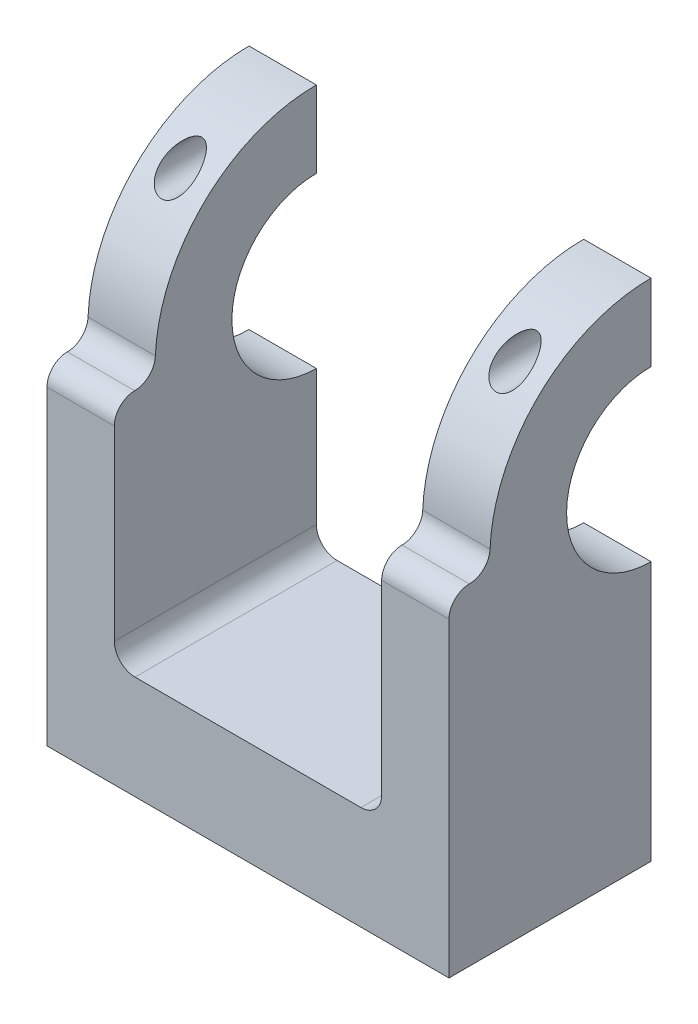
SolidWorks part; units mm, degrees
ref_plane "Front Plane" through (0, 0, 0) normal (0, 0, 1) x (1, 0, 0)
ref_plane "Top Plane" through (0, 0, 0) normal (0, 1, 0) x (1, 0, 0)
ref_plane "Right Plane" through (0, 0, 0) normal (1, 0, 0) x (0, 0, -1)
sketch "Sketch1" plane through (0, 0, 0) normal (1, 0, 0) x (0, 0, -1)
  circle A0 centre (0, 0) radius 8
  dimension "D1" = 16
sketch3d "3DSketch1" plane through (0, 0, 0) normal (0, 0, 1) x (1, 0, 0)
  dimension "D1" = 32.3
sketch "Sketch2" plane through (32.3, 0, 0) normal (1, 0, 0) x (0, 0, -1)
  circle A2 centre (0, 0) radius 8.15
  circle A3 centre (0, 0) radius 15.55
  dimension "D1" = 16.3
  dimension "D2" = 7.4
sketch "Sketch3" plane through (0, 0, 0) normal (1, 0, 0) x (0, 0, -1)
  circle A0 centre (0, 0) radius 8.15
  circle A1 centre (0, 0) radius 15.55
  dimension "D1" = 16.3
  dimension "D2" = 7.4
extrude "Boss-Extrude4" add sketch "Sketch3" along normal blind 6.5 separate body
extrude "Boss-Extrude5" add sketch "Sketch2" along normal blind 6.5
sketch "Sketch4" plane through (0, 0, 0) normal (1, 0, 0) x (0, 0, -1)
  line L0 (0, 15.55) -> (0, -15.55)
  circle A0 centre (0, 0) radius 15.55 construction
  arc A1 (0, -15.55) -> (0, 15.55) centre (0, 0) ccw
extrude "Cut-Extrude1" cut sketch "Sketch4" along normal up to surface (38.8 mm away) up to face at (38.8, 0, -15.55)
sketch "Sketch5" plane through (0, 0, 0) normal (0, 0, -1) x (-1, 0, 0)
  line L0 (-35.55, 15.55) -> (-35.55, 8.15) construction
  line L1 (-38.8, 15.55) -> (-32.3, 15.55) construction
  line L2 (-32.3, 8.15) -> (-38.8, 8.15) construction
  line L3 (-38.8, 11.85) -> (-32.3, 11.85) construction
  line L4 (-38.8, 15.55) -> (-38.8, 8.15) construction
  line L5 (-32.3, 8.15) -> (-32.3, 15.55) construction
  line L6 (-3.25, 15.55) -> (-3.25, 8.15) construction
  line L7 (0, 15.55) -> (-6.5, 15.55) construction
  line L8 (0, 8.15) -> (-6.5, 8.15) construction
  line L9 (-6.5, 11.85) -> (0, 11.85) construction
  line L10 (-6.5, 8.15) -> (-6.5, 15.55) construction
  line L11 (0, 15.55) -> (0, 8.15) construction
  circle A0 centre (-35.55, 11.85) radius 1.6
  circle A1 centre (-3.25, 11.85) radius 1.6
  dimension "D1" = 3.2
  dimension "D2" = 3.2
extrude "Cut-Extrude2" cut sketch "Sketch5" against normal through all
sketch "Sketch6" plane through (32.3, 0, 0) normal (-1, 0, 0) x (0, 0, 1)
  circle A0 centre (0, 0) radius 15.5 construction
  dimension "D1" = 31
sketch "Sketch7" plane through (6.5, 0, 0) normal (1, 0, 0) x (0, 0, -1)
  circle A0 centre (0, 0) radius 19.2 construction
  dimension "D1" = 38.4
sketch "Sketch8" plane through (38.8, 0, 0) normal (1, 0, 0) x (0, 0, -1)
  line L0 (0, 15.55) -> (0, 8.15) construction
  line L1 (0, -8.15) -> (0, -15.55) construction
  line L2 (0, 15.55) -> (0, 8.15)
  line L3 (0, -8.15) -> (0, -15.55)
  line L4 (-15.5, 0) -> (-15.5, -23.2)
  line L5 (0, -15.55) -> (0, -23.2)
  line L6 (-15.5, -23.2) -> (0, -23.2)
  circle A0 centre (0, 0) radius 15.5 construction
  circle A1 centre (0, 0) radius 15.5
  circle A2 centre (0, 0) radius 19.2 construction
  circle A3 centre (0, 0) radius 19.2
  point P7 (-15.5, 0)
  point P14 (0, -19.2)
  arc M1 (0, 15.55) -> (0, -15.55) centre (0, 0) ccw
  dimension "D1" = 4
extrude "Boss-Extrude6" add sketch "Sketch8" against normal up to surface (6.5 mm away) contours A3 L4 L6 L5 | L4 A3 L5 M1 up to face at (32.3, 0, 5.925)
sketch "Sketch9" plane through (0, 0, 15.5) normal (0, 0, 1) x (1, 0, 0)
  line L4 (38.8, -1.246) -> (32.3, -1.246)
  line L5 (32.3, -1.246) -> (32.3, -23.2)
  line L6 (32.3, -23.2) -> (38.8, -23.2)
  line L7 (38.8, -23.2) -> (38.8, -1.246)
  line L10 (32.3, -1.246) -> (32.3, -23.2)
  line L11 (32.3, -23.2) -> (38.8, -23.2)
  line L12 (38.8, -23.2) -> (38.8, -1.246)
  line L15 (38.8, -1.246) -> (32.3, -1.246)
  dimension "D1" = 0
extrude "Boss-Extrude7" add sketch "Sketch9" along normal blind 4
sketch "Sketch11" plane through (0, 0, 0) normal (-1, 0, 0) x (0, 0, 1)
  line L0 (0, -15.55) -> (0, -23.2) construction
  line L1 (15.5, -23.2) -> (0, -23.2) construction
  line L2 (15.5, 0) -> (15.5, -23.2) construction
  line L3 (0, -15.55) -> (0, -23.2)
  line L4 (15.5, -23.2) -> (0, -23.2)
  line L5 (15.5, 0) -> (15.5, -23.2)
  circle A0 centre (0, 0) radius 15.5 construction
  circle A1 centre (0, 0) radius 15.5
  arc M2 (0, -15.55) -> (0, 15.55) centre (0, 0) ccw
extrude "Boss-Extrude8" add sketch "Sketch11" against normal up to surface (6.5 mm away) contours L5 L3 L4 M2 up to face at (6.5, 0, 5.925)
sketch "Sketch12" plane through (0, 0, 15.5) normal (0, 0, 1) x (1, 0, 0)
  line L4 (6.5, -23.2) -> (6.5, -1.246)
  line L5 (6.5, -1.246) -> (0, -1.246)
  line L6 (0, -1.246) -> (0, -23.2)
  line L7 (0, -23.2) -> (6.5, -23.2)
  line L8 (6.5, -23.2) -> (6.5, -1.246)
  line L9 (6.5, -1.246) -> (0, -1.246)
  line L10 (0, -1.246) -> (0, -23.2)
  line L11 (0, -23.2) -> (6.5, -23.2)
  dimension "D1" = 0
extrude "Boss-Extrude9" add sketch "Sketch12" along normal blind 4
fillet "Fillet1" radius 2 1 edges at (35.55, -1.246, 15.5)
fillet "Fillet2" radius 2 1 edges at (3.25, -1.246, 15.5)
sketch "Sketch10" plane through (38.8, 0, 0) normal (1, 0, 0) x (0, 0, -1)
  line L3 (-19.5, -23.2) -> (-19.5, -1.246) construction
  line L4 (-19.5, -3.2122) -> (-19.5, -1.246)
  line L5 (-19.5, -1.246) -> (-17.5338, -1.246)
  arc A1 (-17.5338, -1.246) -> (-15.5356, 0.6681) centre (-17.5338, 0.754) ccw construction
  arc A3 (-17.5338, -1.246) -> (-15.5356, 0.6681) centre (-17.5338, 0.754) ccw
  arc A4 (-17.5338, -1.246) -> (-19.5, -3.2122) centre (-17.5338, -3.2122) ccw
extrude "Cut-Extrude3" cut sketch "Sketch10" against normal through all
sketch "Sketch13" plane through (38.8, 0, 0) normal (1, 0, 0) x (0, 0, -1)
  line L0 (-19.5, -23.2) -> (0, -23.2) construction
  line L1 (-19.5, -23.2) -> (0, -23.2)
  line L2 (-19.5, -23.2) -> (-19.5, -33.2)
  line L3 (-19.5, -33.2) -> (0, -33.2)
  line L4 (0, -33.2) -> (0, -23.2)
  dimension "D1" = 10
extrude "Boss-Extrude10" add sketch "Sketch13" against normal up to surface (38.8 mm away) up to face at (0, -3.9393, 10.4039)
fillet "Fillet3" radius 2 2 edges at (6.5, -23.2, 9.75) (32.3, -23.2, 9.75)
